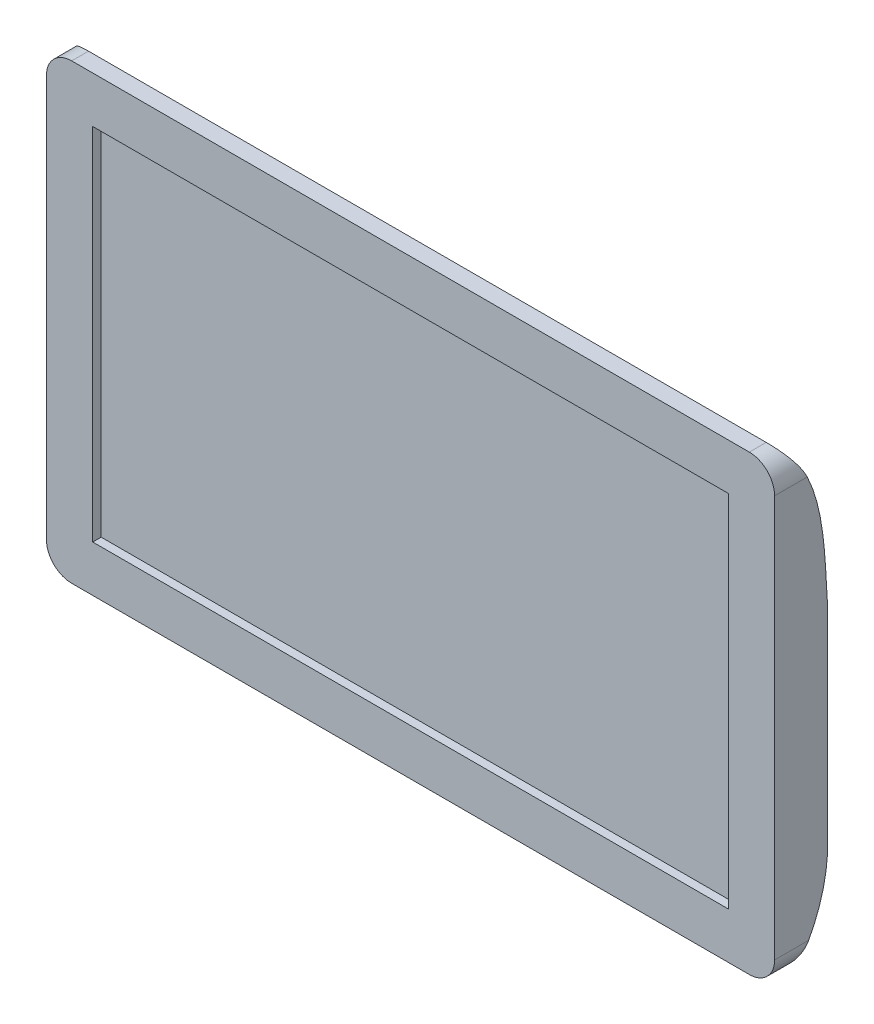
SolidWorks part; units mm, degrees
ref_plane "Front Plane" through (0, 0, 0) normal (0, 0, 1) x (1, 0, 0)
ref_plane "Top Plane" through (0, 0, 0) normal (0, 1, 0) x (1, 0, 0)
ref_plane "Right Plane" through (0, 0, 0) normal (1, 0, 0) x (0, 0, -1)
sketch "Sketch1" plane through (0, 0, 0) normal (0, 0, 1) x (1, 0, 0)
  line L1 (-255.5875, -170.6563) -> (255.5875, -170.6563)
  line L2 (-274.6375, -151.6062) -> (-274.6375, 151.6062)
  line L3 (-255.5875, 170.6562) -> (255.5875, 170.6562)
  line L4 (274.6375, -151.6062) -> (274.6375, 151.6062)
  arc A0 (-255.5875, 170.6562) -> (-274.6375, 151.6062) centre (-255.5875, 151.6062) ccw
  arc A1 (-255.5875, -170.6563) -> (-274.6375, -151.6062) centre (-255.5875, -151.6063) cw
  arc A2 (255.5875, -170.6563) -> (274.6375, -151.6062) centre (255.5875, -151.6063) ccw
  arc A3 (255.5875, 170.6562) -> (274.6375, 151.6062) centre (255.5875, 151.6062) cw
  dimension "D1" = 19.05
  dimension "D2" = 19.05
  dimension "D3" = 19.05
  dimension "D4" = 19.05
extrude "Boss-Extrude1" add sketch "Sketch1" against normal blind 50.8
sketch "Sketch2" plane through (0, 0, 0) normal (0, 0, 1) x (1, 0, 0)
  line L5 (-239.7125, -135.7312) -> (239.7125, -135.7312)
  line L6 (-239.7125, -135.7312) -> (-239.7125, 135.7312)
  line L7 (-239.7125, 135.7312) -> (239.7125, 135.7312)
  line L8 (239.7125, -135.7312) -> (239.7125, 135.7312)
  line L9 (-239.7125, -135.7312) -> (239.7125, 135.7312) construction
  line L10 (-239.7125, 135.7312) -> (239.7125, -135.7312) construction
  point P9 (0, 0)
extrude "Cut-Extrude1" cut sketch "Sketch2" against normal blind 6.35
sketch "Sketch4" plane through (274.6375, 0, 0) normal (1, 0, 0) x (0, 0, -1)
  line L0 (12.7, 170.6562) -> (50.8, 170.6562)
  line L2 (50.8, 170.6562) -> (50.8, 56.2845)
  line L5 (50.8, 56.2845) -> (50.8, -96.1155)
  line L6 (50.8, -96.1155) -> (50.8, -170.6563)
  line L7 (50.8, -170.6563) -> (0, -170.6563) construction
  line L8 (50.8, -170.6563) -> (12.7, -170.6562)
  line L10 (50.8, 56.2845) -> (46.1583, 56.2845)
  line L12 (50.8, -96.1155) -> (46.291, -96.1155)
  arc A0 (39.8203, 62.2448) -> (46.1583, 56.2845) centre (46.1583, 62.6345) ccw
  arc A1 (39.9546, -102.0506) -> (46.291, -96.1155) centre (46.291, -102.4655) cw
  spline S0 degree 3 poles (12.7, 170.6562) (37.5692, 139.578) (37.458, 100.6597) (39.8203, 62.2448) knots 0 0 0 0 0.642402 0.642402 0.642402 0.642402
  spline S1 degree 3 poles (12.7, -170.6563) (29.1155, -150.8148) (38.2705, -127.7717) (39.9546, -102.0506) knots 0 0 0 0 0.929134 0.929134 0.929134 0.929134
  line M8 (50.8, -151.6062) -> (50.8, 151.6062)
  line M9 (50.8, 151.6062) -> (0, 151.6062)
  dimension "D1" = 6.35
  dimension "D2" = 6.35
extrude "Cut-Extrude2" cut sketch "Sketch4" against normal blind 762 contours S0 A0 L10 M9 M8 | L0 S0 L2 M9 | L6 L8 S1 A1 L12
sketch "Sketch6" plane through (0, 0, -50.8) normal (0, 0, -1) x (-1, 0, 0)
  line L0 (-274.6375, 62.2448) -> (-274.6375, -102.0506)
  line L1 (-274.6375, -102.0506) -> (-76.2, -102.0506)
  line L2 (274.6375, -102.0506) -> (274.6375, 62.2448)
  line L3 (274.6375, 62.2448) -> (76.2, 62.2448)
  line L5 (-76.2, 62.2448) -> (-274.6375, 62.2448)
  line L7 (-76.2, -102.0506) -> (-76.2, 62.2448)
  line L9 (76.2, -102.0506) -> (76.2, 62.2448)
  line L12 (76.2, -102.0506) -> (274.6375, -102.0506)
extrude "Cut-Extrude3" cut sketch "Sketch6" against normal blind 10.922
